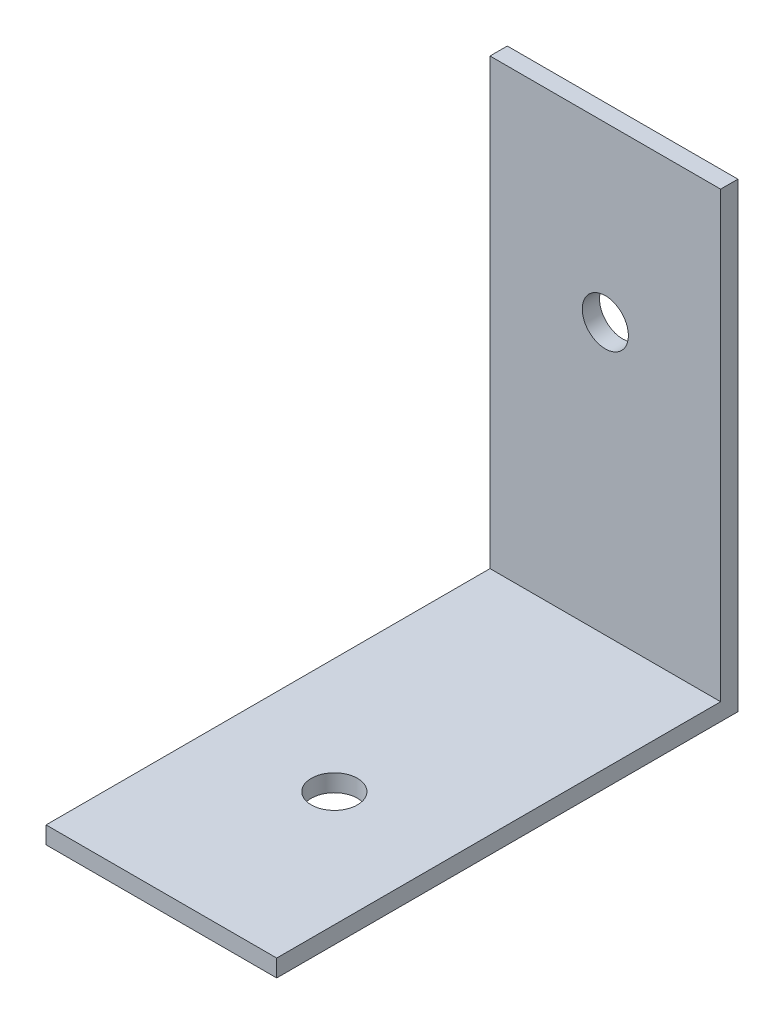
SolidWorks part; units mm, degrees
ref_plane "Front Plane" through (0, 0, 0) normal (0, 0, 1) x (1, 0, 0)
ref_plane "Top Plane" through (0, 0, 0) normal (0, 1, 0) x (1, 0, 0)
ref_plane "Right Plane" through (0, 0, 0) normal (1, 0, 0) x (0, 0, -1)
sketch "Sketch1" plane through (0, 0, 0) normal (0, 1, 0) x (1, 0, 0)
  line L0 (0, 20) -> (0, -5) construction
  line L1 (-10, 20) -> (10, 20)
  line L2 (-10, 20) -> (-10, -20)
  line L3 (-10, -20) -> (10, -20)
  line L4 (10, 20) -> (10, -20)
  line L5 (-10, 20) -> (10, -20) construction
  line L6 (-10, -20) -> (10, 20) construction
  circle A0 centre (0, -5) radius 2
  point P0 (0, 0)
  dimension "D4" = 4
  dimension "D1" = 20
  dimension "D2" = 40
  dimension "D3" = 25
extrude "Boss-Extrude1" add sketch "Sketch1" along normal blind 1.5
sketch "Sketch2" plane through (0, 1.5, 0) normal (0, 1, 0) x (1, 0, 0)
  line L0 (-10, 20) -> (10, 20)
  line L1 (-10, 20) -> (-10, 18.5)
  line L2 (10, 20) -> (10, 18.5)
  line L3 (-10, 18.5) -> (10, 18.5)
  dimension "D1" = 1.5
extrude "Boss-Extrude2" add sketch "Sketch2" along normal blind 38.5 contours L3 L2 L0 L1
sketch "Sketch3" plane through (0, 0, -20) normal (0, 0, -1) x (-1, 0, 0)
  line L0 (0, 0) -> (0, 25) construction
  circle A0 centre (0, 25) radius 2
  dimension "D2" = 4
  dimension "D1" = 25
extrude "Cut-Extrude1" cut sketch "Sketch3" against normal up to surface (1.5 mm away) contours A0 up to face at (0, 20.75, -18.5)
